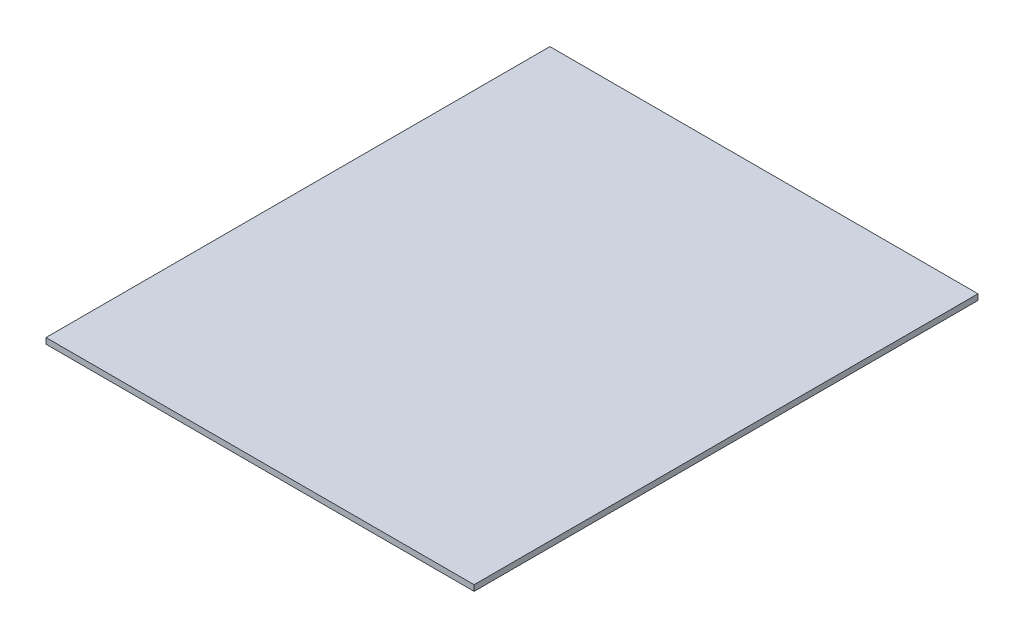
SolidWorks part; units mm, degrees
ref_plane "Front Plane" through (0, 0, 0) normal (0, 0, 1) x (1, 0, 0)
ref_plane "Top Plane" through (0, 0, 0) normal (0, 1, 0) x (1, 0, 0)
ref_plane "Right Plane" through (0, 0, 0) normal (1, 0, 0) x (0, 0, -1)
sketch "Sketch2" plane through (0, 330, 0) normal (0, 1, 0) x (1, 0, 0)
  line L0 (-110.5, 125.5) -> (110.5, 125.5)
  line L1 (110.5, 125.5) -> (110.5, -134.6249)
  line L2 (110.5, -134.6249) -> (-110.5, -134.6249)
  line L3 (-110.5, -134.6249) -> (-110.5, 125.5)
  point P6 (0, 0)
extrude "Boss-Extrude1" add sketch "Sketch2" along normal blind 3
